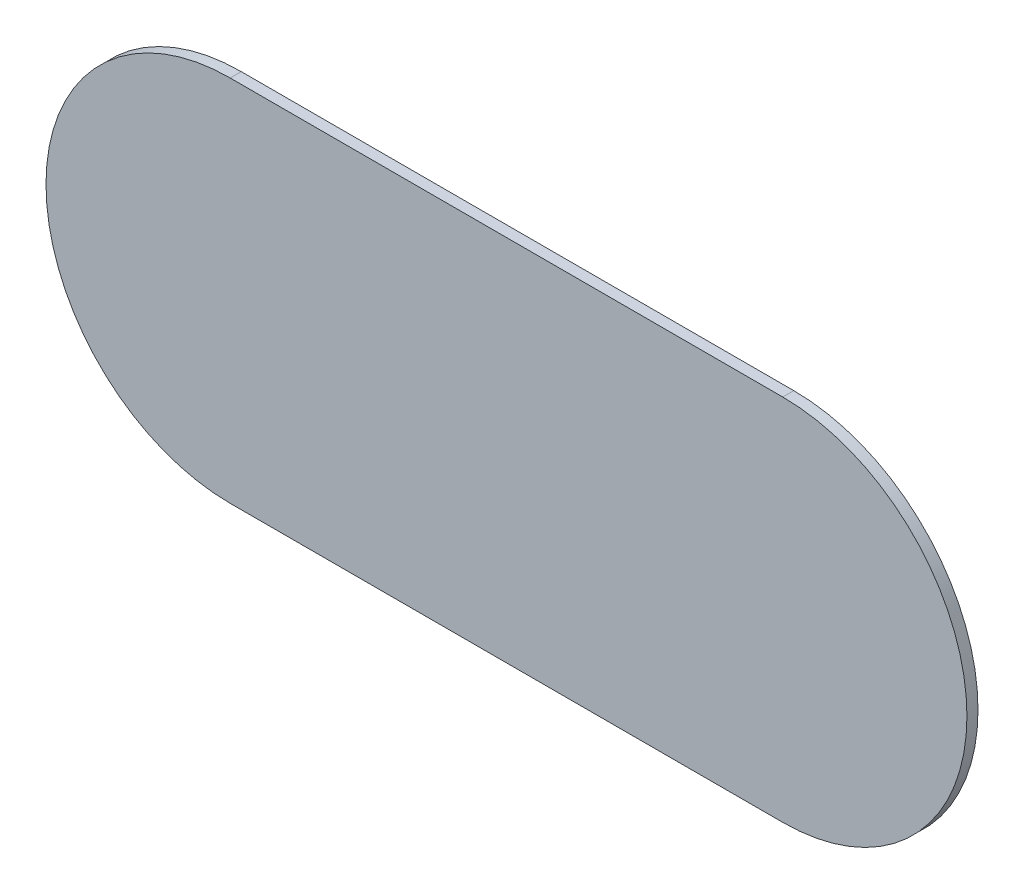
SolidWorks part; units mm, degrees
ref_plane "Front" through (0, 0, 0) normal (0, 0, 1) x (1, 0, 0)
ref_plane "Top" through (0, 0, 0) normal (0, 1, 0) x (1, 0, 0)
ref_plane "Right" through (0, 0, 0) normal (1, 0, 0) x (0, 0, -1)
sketch "Sketch1" plane through (0, 0, 0) normal (0, 0, 1) x (1, 0, 0)
  line L0 (70.9922, 4.5556) -> (145.9922, 4.5556) construction
  line L1 (70.9922, 29.5556) -> (145.9922, 29.5556)
  line L2 (70.9922, -20.4444) -> (145.9922, -20.4444)
  arc A0 (70.9922, 29.5556) -> (70.9922, -20.4444) centre (70.9922, 4.5556) ccw
  arc A1 (145.9922, -20.4444) -> (145.9922, 29.5556) centre (145.9922, 4.5556) ccw
  arc A2 (145.9922, -20.4444) -> (145.9922, 29.5556) centre (145.9922, 4.5556) ccw construction
  arc A3 (70.9922, 29.5556) -> (70.9922, -20.4444) centre (70.9922, 4.5556) ccw construction
  point P3 (108.4922, 4.5556)
extrude "Boss-Extrude1" add sketch "Sketch1" along normal blind 1.5
